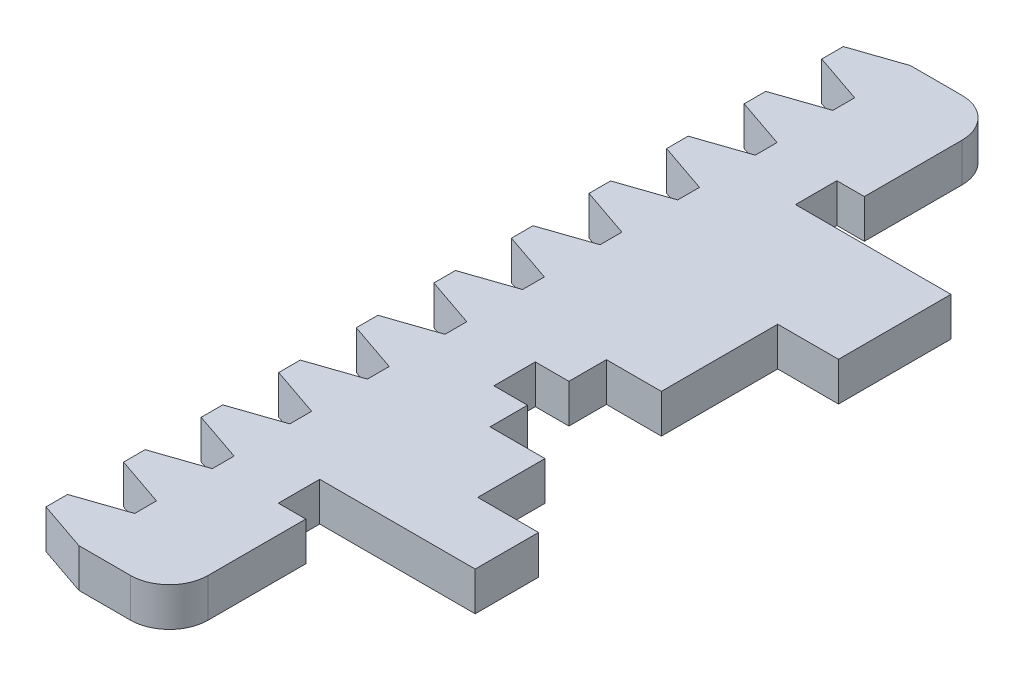
SolidWorks part; units mm, degrees
ref_plane "Front Plane" through (0, 0, 0) normal (0, 0, 1) x (1, 0, 0)
ref_plane "Top Plane" through (0, 0, 0) normal (0, 1, 0) x (1, 0, 0)
ref_plane "Right Plane" through (0, 0, 0) normal (1, 0, 0) x (0, 0, -1)
sketch "Sketch1" plane through (0, 0, 0) normal (0, 1, 0) x (1, 0, 0)
  line L4 (37.95, 21.5) -> (28.05, 21.5) construction
  line L5 (28.05, 29.157) -> (28.05, 21.5) construction
  line L6 (21.0585, 32.157) -> (25.05, 32.157) construction
  line L7 (21.0585, 32.157) -> (17.1887, 30.8335) construction
  line L8 (17.1887, 30.8335) -> (17.1887, 29.1665) construction
  line L13 (17.1887, 29.1665) -> (21.0585, 27.843) construction
  line L14 (21.0585, 26.157) -> (21.0585, 27.843) construction
  line L15 (21.0585, 26.157) -> (17.1887, 24.8335) construction
  line L16 (17.1887, 24.8335) -> (17.1887, 23.1665) construction
  line L17 (17.1887, 23.1665) -> (21.0585, 21.843) construction
  line L18 (21.0585, 20.157) -> (21.0585, 21.843) construction
  line L19 (21.0585, 20.157) -> (17.1887, 18.8335) construction
  line L20 (17.1887, 18.8335) -> (17.1887, 17.1665) construction
  line L21 (17.1887, 17.1665) -> (21.0585, 15.843) construction
  line L22 (21.0585, 14.157) -> (21.0585, 15.843) construction
  line L23 (21.0585, 14.157) -> (17.1887, 12.8335) construction
  line L24 (17.1887, 12.8335) -> (17.1887, 11.1665) construction
  line L25 (17.1887, 11.1665) -> (21.0585, 9.843) construction
  line L26 (21.0585, 8.157) -> (21.0585, 9.843) construction
  line L27 (21.0585, 8.157) -> (17.1887, 6.8335) construction
  line L28 (17.1887, 6.8335) -> (17.1887, 5.1665) construction
  line L29 (17.1887, 5.1665) -> (21.0585, 3.843) construction
  line L30 (21.0585, 2.157) -> (21.0585, 3.843) construction
  line L31 (21.0585, 2.157) -> (17.1887, 0.8335) construction
  line L32 (17.1887, 0.8335) -> (17.1887, -0.8335) construction
  line L33 (17.1887, -0.8335) -> (21.0585, -2.157) construction
  line L34 (21.0585, -3.843) -> (21.0585, -2.157) construction
  line L35 (21.0585, -3.843) -> (17.1887, -5.1665) construction
  line L36 (17.1887, -5.1665) -> (17.1887, -6.8335) construction
  line L37 (17.1887, -6.8335) -> (21.0585, -8.157) construction
  line L38 (21.0585, -9.843) -> (21.0585, -8.157) construction
  line L39 (21.0585, -9.843) -> (17.1887, -11.1665) construction
  line L40 (17.1887, -11.1665) -> (17.1887, -12.8335) construction
  line L41 (17.1887, -12.8335) -> (21.0585, -14.157) construction
  line L42 (21.0585, -15.843) -> (21.0585, -14.157) construction
  line L43 (21.0585, -15.843) -> (17.1887, -17.1665) construction
  line L44 (17.1887, -17.1665) -> (17.1887, -18.8335) construction
  line L45 (17.1887, -18.8335) -> (21.0585, -20.157) construction
  line L46 (21.0585, -21.843) -> (21.0585, -20.157) construction
  line L47 (21.0585, -21.843) -> (17.1887, -23.1665) construction
  line L48 (17.1887, -23.1665) -> (17.1887, -24.8335) construction
  line L49 (17.1887, -24.8335) -> (21.0585, -26.157) construction
  line L55 (21.0585, -27.843) -> (21.0585, -26.157) construction
  line L56 (21.0585, -27.843) -> (17.1887, -29.1665) construction
  line L57 (17.1887, -29.1665) -> (17.1887, -30.8335) construction
  line L99 (17.1887, -30.8335) -> (21.0585, -32.157) construction
  line L100 (25.05, -32.157) -> (21.0585, -32.157) construction
  line L105 (28.05, -21.5) -> (28.05, -29.157) construction
  line L107 (37.95, -21.5) -> (28.05, -21.5) construction
  line L108 (37.95, -8.3) -> (37.95, -21.5) construction
  line L109 (29, -8.3) -> (37.95, -8.3) construction
  line L110 (29, 0.7) -> (29, -8.3) construction
  line L111 (37.95, 0.7) -> (29, 0.7) construction
  line L112 (37.95, 21.5) -> (37.95, 0.7) construction
  line L113 (37.95, 21.5) -> (28.05, 21.5)
  line L114 (28.05, 29.157) -> (28.05, 21.5)
  line L115 (21.0585, 32.157) -> (25.05, 32.157)
  line L116 (21.0585, 32.157) -> (17.1887, 30.8335)
  line L117 (17.1887, 30.8335) -> (17.1887, 29.1665)
  line L118 (17.1887, 29.1665) -> (21.0585, 27.843)
  line L119 (21.0585, 26.157) -> (21.0585, 27.843)
  line L120 (21.0585, 26.157) -> (17.1887, 24.8335)
  line L121 (17.1887, 24.8335) -> (17.1887, 23.1665)
  line L122 (17.1887, 23.1665) -> (21.0585, 21.843)
  line L123 (21.0585, 20.157) -> (21.0585, 21.843)
  line L124 (21.0585, 20.157) -> (17.1887, 18.8335)
  line L125 (17.1887, 18.8335) -> (17.1887, 17.1665)
  line L126 (17.1887, 17.1665) -> (21.0585, 15.843)
  line L127 (21.0585, 14.157) -> (21.0585, 15.843)
  line L128 (21.0585, 14.157) -> (17.1887, 12.8335)
  line L129 (17.1887, 12.8335) -> (17.1887, 11.1665)
  line L130 (17.1887, 11.1665) -> (21.0585, 9.843)
  line L131 (21.0585, 8.157) -> (21.0585, 9.843)
  line L132 (21.0585, 8.157) -> (17.1887, 6.8335)
  line L133 (17.1887, 6.8335) -> (17.1887, 5.1665)
  line L134 (17.1887, 5.1665) -> (21.0585, 3.843)
  line L135 (21.0585, 2.157) -> (21.0585, 3.843)
  line L136 (21.0585, 2.157) -> (17.1887, 0.8335)
  line L137 (17.1887, 0.8335) -> (17.1887, -0.8335)
  line L138 (17.1887, -0.8335) -> (21.0585, -2.157)
  line L139 (21.0585, -3.843) -> (21.0585, -2.157)
  line L140 (21.0585, -3.843) -> (17.1887, -5.1665)
  line L141 (17.1887, -5.1665) -> (17.1887, -6.8335)
  line L142 (17.1887, -6.8335) -> (21.0585, -8.157)
  line L143 (21.0585, -9.843) -> (21.0585, -8.157)
  line L144 (21.0585, -9.843) -> (17.1887, -11.1665)
  line L145 (17.1887, -11.1665) -> (17.1887, -12.8335)
  line L146 (17.1887, -12.8335) -> (21.0585, -14.157)
  line L147 (21.0585, -15.843) -> (21.0585, -14.157)
  line L148 (21.0585, -15.843) -> (17.1887, -17.1665)
  line L149 (17.1887, -17.1665) -> (17.1887, -18.8335)
  line L150 (17.1887, -18.8335) -> (21.0585, -20.157)
  line L151 (21.0585, -21.843) -> (21.0585, -20.157)
  line L152 (21.0585, -21.843) -> (17.1887, -23.1665)
  line L153 (17.1887, -23.1665) -> (17.1887, -24.8335)
  line L154 (17.1887, -24.8335) -> (21.0585, -26.157)
  line L155 (21.0585, -27.843) -> (21.0585, -26.157)
  line L156 (21.0585, -27.843) -> (17.1887, -29.1665)
  line L157 (17.1887, -29.1665) -> (17.1887, -30.8335)
  line L160 (17.1887, -30.8335) -> (21.0585, -32.157)
  line L161 (25.05, -32.157) -> (21.0585, -32.157)
  line L162 (28.05, -21.5) -> (28.05, -29.157)
  line L163 (37.95, -21.5) -> (28.05, -21.5)
  line L164 (37.95, -8.3) -> (37.95, -21.5)
  line L165 (29, -8.3) -> (37.95, -8.3)
  line L166 (29, 0.7) -> (29, -8.3)
  line L167 (37.95, 0.7) -> (29, 0.7)
  line L168 (37.95, 21.5) -> (37.95, 0.7)
  line L169 (37.95, 28.5) -> (33.35, 28.5) construction
  line L170 (15.05, 32.157) -> (26.5, 32.157) construction
  line L171 (15.05, 32.157) -> (15.05, -32.157) construction
  line L172 (15.05, -32.157) -> (26.5, -32.157) construction
  line L173 (19.65, 32.157) -> (19.65, -32.157) construction
  line L174 (37.95, 28.5) -> (33.35, 28.5) construction
  line L175 (37.95, 28.5) -> (37.95, -28.5) construction
  line L176 (37.95, -28.5) -> (33.35, -28.5) construction
  line L177 (33.35, 28.5) -> (33.35, -28.5) construction
  line L178 (21.0585, 32.157) -> (15.05, 32.157) construction
  line L179 (15.05, -32.157) -> (21.0585, -32.157) construction
  line L180 (15.05, 32.157) -> (15.05, -32.157) construction
  line L181 (19.65, -32.157) -> (19.65, 32.157) construction
  line L182 (37.95, -28.5) -> (33.35, -28.5) construction
  line L183 (33.35, -28.5) -> (33.35, 28.5) construction
  line L184 (37.95, 28.5) -> (37.95, -28.5) construction
  line L185 (37.95, 0) -> (15.05, 0) construction
  line L186 (15.05, 0) -> (37.95, 0) construction
  line L187 (26.5, 32.157) -> (26.5, -32.157) construction
  line L188 (26.5, 32.157) -> (26.5, -32.157) construction
  line L189 (19.65, 21.5) -> (37.95, 21.5) construction
  line L190 (19.65, -21.5) -> (37.95, -21.5) construction
  line L191 (37.95, 21.5) -> (19.65, 21.5) construction
  line L192 (37.95, -2.3) -> (32, -2.3) construction
  line L193 (32, -2.3) -> (32, -5.3) construction
  line L194 (32, -5.3) -> (37.95, -5.3) construction
  line L195 (29, -3.8) -> (37.95, -3.8) construction
  line L196 (34.95, 0.7) -> (34.95, 18.5) construction
  line L197 (34.95, -8.3) -> (34.95, -18.5) construction
  line L198 (34.95, 18.5) -> (19.65, 18.5) construction
  line L199 (19.65, -18.5) -> (34.95, -18.5) construction
  line L200 (34.95, 18.5) -> (34.95, 21.5) construction
  line L201 (34.95, 18.5) -> (37.95, 18.5) construction
  line L202 (34.95, -18.5) -> (37.95, -18.5) construction
  line L203 (34.95, -18.5) -> (34.95, -21.5) construction
  line L204 (37.15, 28.5) -> (37.15, -28.5) construction
  line L205 (34.15, 28.5) -> (34.15, -28.5) construction
  line L206 (18.85, 32.157) -> (18.85, -32.157) construction
  line L207 (15.85, 32.157) -> (15.85, -32.157) construction
  line L208 (37.15, 28.5) -> (37.15, 0.7) construction
  line L209 (34.15, 28.5) -> (34.15, 0.7) construction
  line L210 (18.85, 32.157) -> (18.85, -32.157) construction
  line L211 (15.85, 32.157) -> (15.85, -32.157) construction
  line L212 (37.15, -8.3) -> (37.15, -28.5) construction
  line L213 (34.15, -8.3) -> (34.15, -28.5) construction
  arc A2 (28.05, 29.157) -> (25.05, 32.157) centre (25.05, 29.157) ccw construction
  arc A3 (25.05, -32.157) -> (28.05, -29.157) centre (25.05, -29.157) ccw construction
  arc A4 (28.05, 29.157) -> (25.05, 32.157) centre (25.05, 29.157) ccw
  arc A5 (25.05, -32.157) -> (28.05, -29.157) centre (25.05, -29.157) ccw
sketch "Sketch2" plane through (0, 0, 0) normal (0, 0, 1) x (1, 0, 0)
  line L1 (37.95, -3) -> (15.05, -3)
  line L2 (37.95, -3) -> (37.95, 0)
  line L3 (37.95, 0) -> (15.05, 0)
  line L4 (15.05, -3) -> (15.05, 0)
  line L5 (21, -3) -> (-21, -3) construction
extrude "Boss-Extrude1" add sketch "Sketch1" against normal up to vertex (3 mm away) up to point (15.05, -3, 0)
ref_plane "gear" through (0, 0, 2.3) normal (0, 0, 1) x (1, 0, 0)
ref_plane "front" through (0, 0, 21.5) normal (0, 0, 1) x (1, 0, 0)
ref_plane "back" through (0, 0, -21.5) normal (0, 0, 1) x (1, 0, 0)
ref_plane "top" through (37.15, 0, 0) normal (1, 0, 0) x (0, 0, -1)
ref_plane "bottom" through (15.85, 0, 0) normal (1, 0, 0) x (0, 0, -1)
ref_plane "sym" through (26.5, 0, 0) normal (1, 0, 0) x (0, 0, -1)
sketch "Sketch3" plane through (0, 0, 0) normal (0, 1, 0) x (1, 0, 0)
  line L0 (37.95, 21.5) -> (37.95, 0.7) construction
  line L1 (37.95, 21.5) -> (19.65, 21.5) construction
  line L2 (37.95, 21.5) -> (37.95, 0.7) construction
  line L3 (37.95, -21.5) -> (19.65, -21.5) construction
  line L4 (19.65, 21.5) -> (19.65, -21.5) construction
  line L5 (37.95, 21.5) -> (28.05, 21.5) construction
  line L6 (37.95, -21.5) -> (28.05, -21.5) construction
  line L7 (19.65, 32.157) -> (19.65, -32.157) construction
  line L8 (37.95, 18.5) -> (19.65, 18.5) construction
  line L9 (37.95, -18.5) -> (19.65, -18.5) construction
  line L10 (19.65, -18.5) -> (34.95, -18.5) construction
  line L11 (34.95, 18.5) -> (19.65, 18.5) construction
  line L12 (37.95, 0.7) -> (29, 0.7) construction
  line L13 (29, 0.7) -> (29, -8.3) construction
  line L14 (29, -8.3) -> (37.95, -8.3) construction
  line L15 (29, 0.7) -> (29, -8.3) construction
  line L16 (29, -8.3) -> (37.95, -8.3) construction
  line L17 (37.95, 0.7) -> (29, 0.7) construction
  line L18 (37.95, -8.3) -> (37.95, -21.5) construction
  line L19 (26.025, -18.5) -> (26.025, -21.5)
  line L20 (26.025, 21.5) -> (26.025, 18.5)
  line L21 (33.35, 28.5) -> (33.35, -28.5) construction
  line L22 (37.95, 9.6) -> (33.35, 9.6)
  line L23 (37.95, 9.6) -> (37.95, -13.4)
  line L24 (37.95, -13.4) -> (33.35, -13.4)
  line L25 (33.35, 9.6) -> (33.35, -13.4)
  line L26 (37.95, 28.5) -> (37.95, -28.5) construction
  line L27 (37.95, -13.4) -> (33.35, -13.4) construction
  line L28 (37.95, 9.6) -> (33.35, 9.6) construction
  line L29 (26.025, 18.5) -> (37.95, 18.5)
  line L30 (37.95, 18.5) -> (37.95, 21.5)
  line L31 (37.95, 21.5) -> (26.025, 21.5)
  line L32 (26.025, -18.5) -> (37.95, -18.5)
  line L33 (37.95, -18.5) -> (37.95, -21.5)
  line L34 (37.95, -21.5) -> (26.025, -21.5)
  line L35 (26.5, 32.157) -> (26.5, -32.157) construction
  line L36 (26.5, -2.3) -> (29, -2.3)
  line L37 (26.5, -2.3) -> (26.5, -5.3)
  line L38 (26.5, -5.3) -> (29, -5.3)
  line L39 (29, -2.3) -> (29, -5.3)
  line L40 (26.5, 32.157) -> (26.5, -32.157) construction
  line L41 (32, -5.3) -> (37.95, -5.3) construction
  line L42 (37.95, -2.3) -> (32, -2.3) construction
sketch "Sketch4" plane through (0, 0, 0) normal (0, 1, 0) x (1, 0, 0)
  line L0 (25.925, -18.4) -> (25.925, -21.6)
  line L1 (25.925, -21.6) -> (38.05, -21.6)
  line L2 (38.05, -21.6) -> (38.05, -18.4)
  line L3 (38.05, -18.4) -> (25.925, -18.4)
  line L4 (26.025, -18.5) -> (26.025, -21.5)
  line L5 (26.025, -21.5) -> (37.95, -21.5)
  line L6 (37.95, -21.5) -> (37.95, -18.5)
  line L7 (37.95, -18.5) -> (26.025, -18.5)
  line L8 (26.025, -18.5) -> (26.025, -21.5) construction
  line L9 (26.025, -21.5) -> (37.95, -21.5) construction
  line L10 (37.95, -21.5) -> (37.95, -18.5) construction
  line L11 (37.95, -18.5) -> (26.025, -18.5) construction
  line L12 (37.95, 9.6) -> (33.35, 9.6)
  line L13 (33.35, 9.6) -> (33.35, -13.4)
  line L14 (33.35, -13.4) -> (37.95, -13.4)
  line L15 (37.95, -13.4) -> (37.95, 9.6)
  line L16 (37.95, 9.6) -> (33.35, 9.6) construction
  line L17 (33.35, 9.6) -> (33.35, -13.4) construction
  line L18 (33.35, -13.4) -> (37.95, -13.4) construction
  line L19 (37.95, -13.4) -> (37.95, 9.6) construction
  line L20 (26.025, 21.5) -> (26.025, 18.5)
  line L21 (26.025, 18.5) -> (37.95, 18.5)
  line L22 (37.95, 18.5) -> (37.95, 21.5)
  line L23 (37.95, 21.5) -> (26.025, 21.5)
  line L24 (26.025, 21.5) -> (26.025, 18.5) construction
  line L25 (26.025, 18.5) -> (37.95, 18.5) construction
  line L26 (37.95, 18.5) -> (37.95, 21.5) construction
  line L27 (37.95, 21.5) -> (26.025, 21.5) construction
  line L28 (29, -2.3) -> (26.5, -2.3)
  line L29 (26.5, -2.3) -> (26.5, -5.3)
  line L30 (26.5, -5.3) -> (29, -5.3)
  line L31 (29, -5.3) -> (29, -2.3)
  line L32 (29, -2.3) -> (26.5, -2.3) construction
  line L33 (26.5, -2.3) -> (26.5, -5.3) construction
  line L34 (26.5, -5.3) -> (29, -5.3) construction
  line L35 (29, -5.3) -> (29, -2.3) construction
  line L36 (38.05, 9.7) -> (33.25, 9.7)
  line L37 (33.25, 9.7) -> (33.25, -13.5)
  line L38 (33.25, -13.5) -> (38.05, -13.5)
  line L39 (38.05, -13.5) -> (38.05, 9.7)
  line L40 (25.925, 21.6) -> (25.925, 18.4)
  line L41 (25.925, 18.4) -> (38.05, 18.4)
  line L42 (38.05, 18.4) -> (38.05, 21.6)
  line L43 (38.05, 21.6) -> (25.925, 21.6)
  line L44 (29.1, -2.2) -> (26.4, -2.2)
  line L45 (26.4, -2.2) -> (26.4, -5.4)
  line L46 (26.4, -5.4) -> (29.1, -5.4)
  line L47 (29.1, -5.4) -> (29.1, -2.2)
  dimension "D1" = 0
  dimension "D2" = 0
  dimension "D3" = 0
  dimension "D4" = 0
  dimension "D5" = 0.1
extrude "Cut-Extrude1" cut sketch "Sketch4" against normal through all
